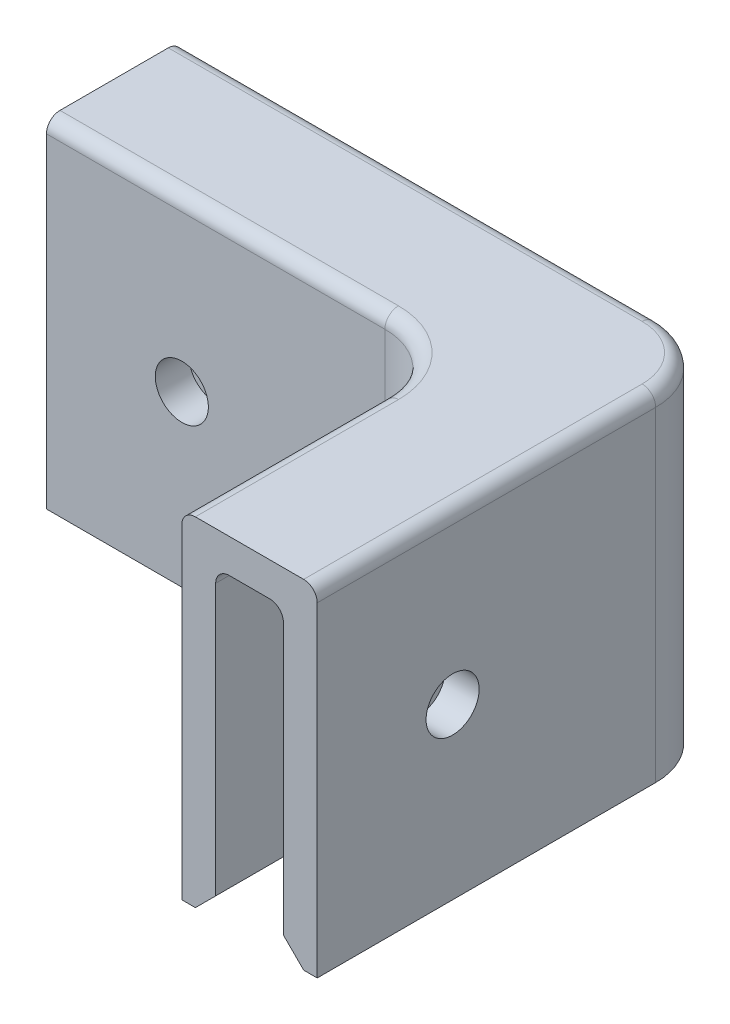
SolidWorks part; units mm, degrees
ref_plane "Front Plane" through (0, 0, 0) normal (0, 0, 1) x (1, 0, 0)
ref_plane "Top Plane" through (0, 0, 0) normal (0, 1, 0) x (1, 0, 0)
ref_plane "Right Plane" through (0, 0, 0) normal (1, 0, 0) x (0, 0, -1)
sketch "Sketch1" plane through (0, 0, 0) normal (0, 1, 0) x (1, 0, 0)
  line L0 (0, 0) -> (0, -38.1)
  line L1 (0, -38.1) -> (-12.7, -38.1)
  line L2 (-12.7, -38.1) -> (-12.7, -12.7)
  line L3 (-12.7, -12.7) -> (-50.8, -12.7)
  line L4 (-50.8, -12.7) -> (-50.8, 0)
  line L5 (-50.8, 0) -> (0, 0)
  point P5 (-8.0946, -8.7254)
  dimension "D1" = 38.1
  dimension "D2" = 50.8
  dimension "D3" = 12.7
extrude "Boss-Extrude1" add sketch "Sketch1" along normal blind 31.75
fillet "Fillet1" radius 6.35 2 edges at (0, 15.875, 0) (-12.7, 15.875, 12.7)
shell "Shell1" thickness 3.175
sketch "Sketch3" plane through (-12.7, 0, 0) normal (-1, 0, 0) x (0, 0, 1)
  line L0 (38.1, 31.75) -> (38.1, 0) construction
  point P0 (25.4, 15.875)
  point P1 (0, 0)
  point P2 (0, 0)
  point P5 (38.1, 15.875)
  dimension "D1" = 12.7
sketch "Sketch4" plane through (0, 0, 12.7) normal (0, 0, 1) x (1, 0, 0)
  line L0 (-50.8, 31.75) -> (-50.8, 0) construction
  point P0 (-38.1, 15.875)
  point P3 (-50.8, 15.875)
  point P4 (0, 0)
  dimension "D1" = 12.7
hole_wizard "#9 (0.196) Diameter Hole1" positions "Sketch3" profile "Sketch5" hole size "#9" standard "ANSI Inch" end condition through all
sketch "Sketch5" plane through (-12.7, 15.875, 25.4) normal (0, 1, 0) x (0, 0, 1)
  line L0 (0, 0) -> (0, 12.7)
  line L1 (0, 12.7) -> (2.4892, 12.7)
  line L2 (2.4892, 12.7) -> (2.4892, 0)
  line L5 (2.4892, 0) -> (0, 0)
  line L11 (0, -6.35) -> (0, 107.95) construction
  dimension "Thru Hole Dia." = 4.9784
  dimension "Thru Hole Depth" = 12.7
hole_wizard "#9 (0.196) Diameter Hole2" positions "Sketch4" profile "Sketch6" hole size "#9" standard "ANSI Inch" end condition through all
sketch "Sketch6" plane through (-38.1, 15.875, 12.7) normal (1, 0, 0) x (0, -1, 0)
  line L0 (0, 0) -> (0, 12.7)
  line L1 (0, 12.7) -> (2.4892, 12.7)
  line L2 (2.4892, 12.7) -> (2.4892, 0)
  line L5 (2.4892, 0) -> (0, 0)
  line L11 (0, -6.35) -> (0, 107.95) construction
  dimension "Thru Hole Dia." = 4.9784
  dimension "Thru Hole Depth" = 12.7
chamfer "Chamfer1" distance 1.905 angle 45 6 edges at (-28.575, 0, 3.175) (-4.1049, 0, 4.1049) (-3.175, 0, 22.225) (-34.925, 0, 9.525) (-12.3148, 0, 12.3148) (-9.525, 0, 28.575)
fillet "Fillet2" radius 1.27 12 edges at (-28.575, 31.75, 0) (-1.8599, 31.75, 1.8599) (-34.925, 31.75, 12.7) (-14.5599, 31.75, 14.5599) (-28.575, 28.575, 3.175) (-4.1049, 28.575, 4.1049) (-34.925, 28.575, 9.525) (-12.3148, 28.575, 12.3148) (0, 31.75, 22.225) (-12.7, 31.75, 28.575) (-3.175, 28.575, 22.225) (-9.525, 28.575, 28.575)
